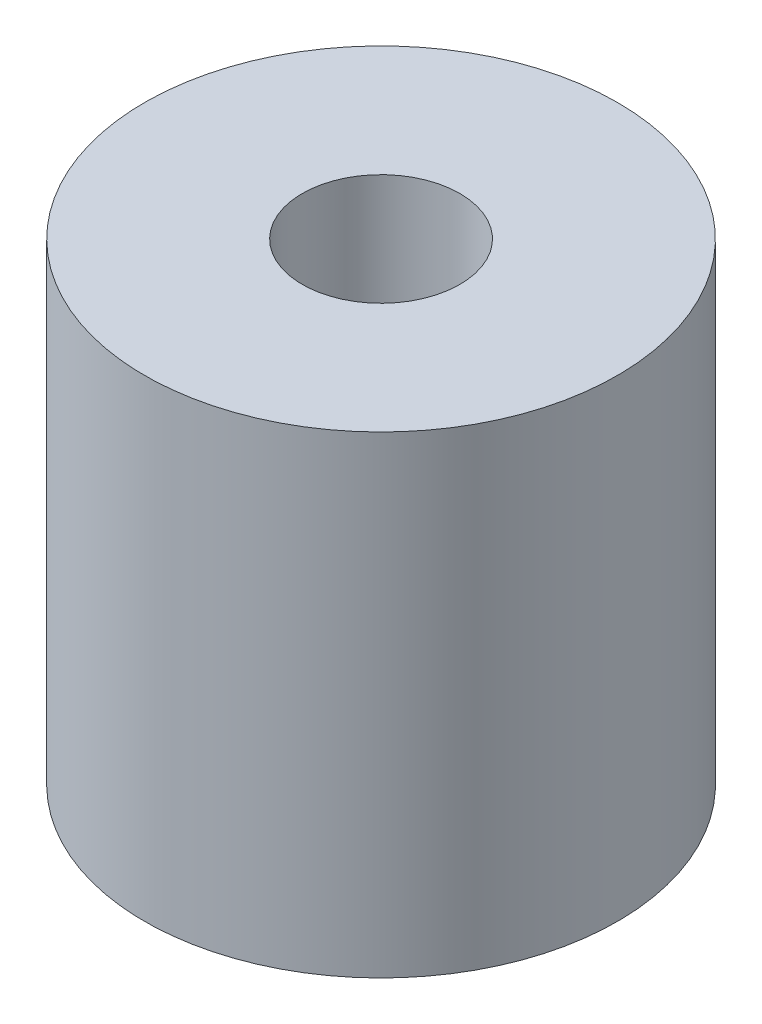
SolidWorks part; units mm, degrees
ref_plane "Спереди" through (0, 0, 0) normal (0, 0, 1) x (1, 0, 0)
ref_plane "Сверху" through (0, 0, 0) normal (0, 1, 0) x (1, 0, 0)
ref_plane "Справа" through (0, 0, 0) normal (1, 0, 0) x (0, 0, -1)
sketch "Эскиз1" plane through (0, 0, 0) normal (0, 0, 1) x (1, 0, 0)
  line L0 (10, 0) -> (10, 60)
  line L1 (10, 60) -> (23.4146, 60)
  line L3 (23.4146, 60) -> (30, 60)
  line L4 (30, 60) -> (30, 0)
  line L5 (30, 0) -> (23.4146, 0)
  line L7 (23.4146, 0) -> (10, 0)
  line L8 (0, -14.7929) -> (0, 77.5948) construction
revolve "Повернуть1" add sketch "Эскиз1" angle 360 about L8
